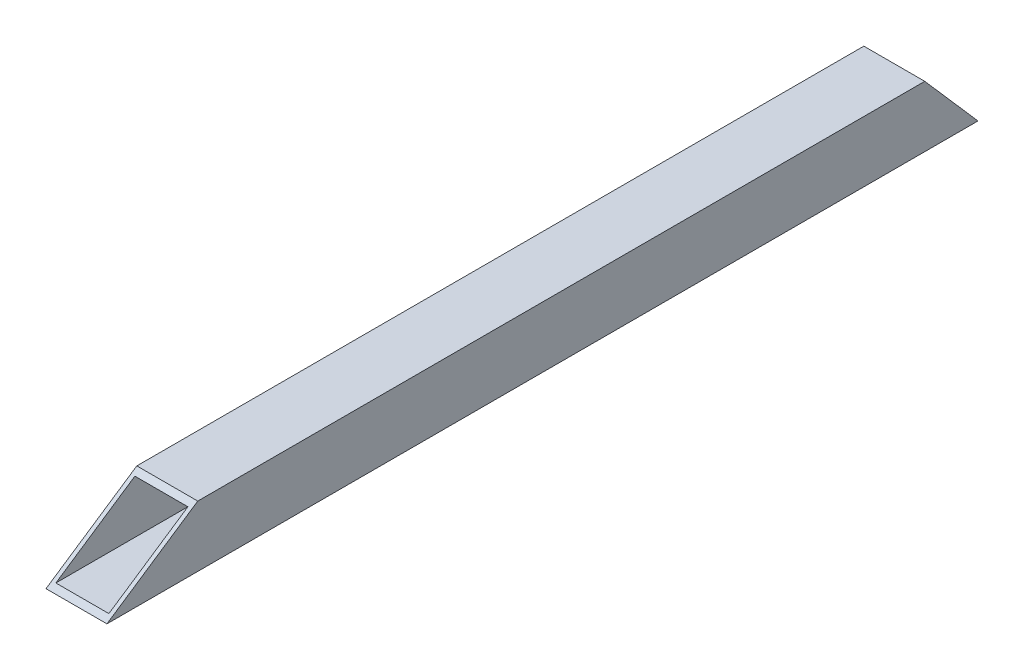
SolidWorks part; units mm, degrees
ref_plane "Front Plane" through (0, 0, 0) normal (0, 0, 1) x (1, 0, 0)
ref_plane "Top Plane" through (0, 0, 0) normal (0, 1, 0) x (1, 0, 0)
ref_plane "Right Plane" through (0, 0, 0) normal (1, 0, 0) x (0, 0, -1)
sketch "Sketch1" plane through (0, 0, 0) normal (0, 0, 1) x (1, 0, 0)
  line L1 (11.049, 11.049) -> (-11.049, 11.049)
  line L2 (11.049, 11.049) -> (11.049, -11.049)
  line L3 (11.049, -11.049) -> (-11.049, -11.049)
  line L4 (-11.049, 11.049) -> (-11.049, -11.049)
  line L5 (11.049, 11.049) -> (-11.049, -11.049) construction
  line L6 (11.049, -11.049) -> (-11.049, 11.049) construction
  line L7 (12.7, 12.7) -> (-12.7, 12.7)
  line L8 (12.7, 12.7) -> (12.7, -12.7)
  line L9 (12.7, -12.7) -> (-12.7, -12.7)
  line L10 (-12.7, 12.7) -> (-12.7, -12.7)
  line L11 (12.7, 12.7) -> (-12.7, -12.7) construction
  line L12 (12.7, -12.7) -> (-12.7, 12.7) construction
  point P0 (0, 0)
  point P6 (0, 0)
  dimension "D3" = 1.651
  dimension "D4" = 1.651
  dimension "D5" = 1.651
  dimension "D2" = 25.4
  dimension "D1" = 25.4
extrude "Boss-Extrude1" add sketch "Sketch1" along normal up to vertex (365.443 mm away)
sketch "Sketch3" plane through (0, 0, 0) normal (0, 1, 0) x (1, 0, 0)
  line L0 (0, 12.8662) -> (0, -262.1311) construction
  line L1 (0, -13.97) -> (0, 13.97) construction
ref_point "Point1"
ref_plane "Plane1" through (0, 132.2171, 169.9007) normal (0, 0.5572, -0.8304) x (-1, 0, 0)
sketch "Sketch5" plane through (0, 132.2171, 169.9007) normal (0, 0.5572, -0.8304) x (-1, 0, 0)
  line L1 (-12.7, 12.7) -> (12.7, 12.7)
  line L2 (-12.7, 12.7) -> (-12.7, -12.7)
  line L3 (-12.7, -12.7) -> (12.7, -12.7)
  line L4 (12.7, 12.7) -> (12.7, -12.7)
  line L5 (-12.7, 12.7) -> (12.7, -12.7) construction
  line L6 (-12.7, -12.7) -> (12.7, 12.7) construction
  point P0 (0, 0)
  dimension "D1" = 25.4
  dimension "D2" = 25.4
extrude "Cut-Extrude2" cut sketch "Sketch5" against normal through all
sketch "Sketch6" plane through (-12.7, 0, 0) normal (-1, 0, 0) x (0, 0, 1)
  line L0 (0, -12.7) -> (25.9871, 17.0482)
  line L1 (25.9871, 17.0482) -> (0, 20.8232)
  line L2 (0, 20.8232) -> (0, -12.7)
  dimension "D1" = 41.14
extrude "Cut-Extrude3" cut sketch "Sketch6" against normal through all
equation "\"c1c2Len\"= 250"
equation "\"D1\"= \"c1c2Len\""
equation "\"1inchSquareTubeLen\"=25.4"
equation "\"D2@Sketch1\"=\"1inchSquareTubeLen\""
equation "\"D1@Sketch1\"=\"1inchSquareTubeLen\""
equation "\"squareTubeWallThickness\"=1.651"
equation "\"D5@Sketch1\"=\"squareTubeWallThickness\""
equation "\"D4@Sketch1\"=\"squareTubeWallThickness\""
equation "\"D3@Sketch1\"=\"squareTubeWallThickness\""
equation "\"D1@Sketch6\"=90-arccos(250/380)"
